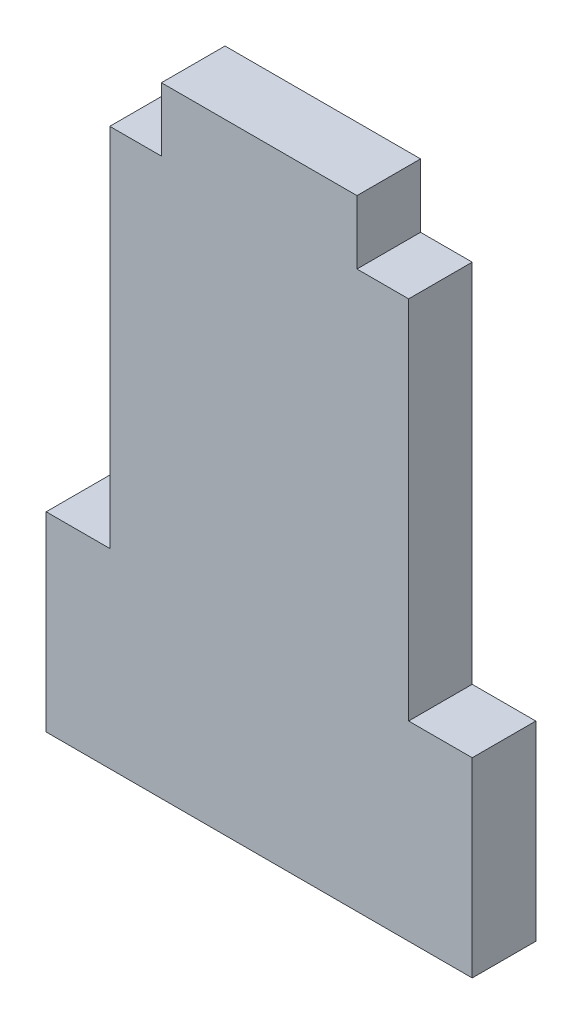
SolidWorks part; units mm, degrees
ref_plane "Ebene vorne" through (0, 0, 0) normal (0, 0, 1) x (1, 0, 0)
ref_plane "Ebene oben" through (0, 0, 0) normal (0, 1, 0) x (1, 0, 0)
ref_plane "Ebene rechts" through (0, 0, 0) normal (1, 0, 0) x (0, 0, -1)
sketch "Skizze1" plane through (0, 0, 0) normal (0, 0, 1) x (1, 0, 0)
  line L0 (0, 0) -> (0, 52.5861) construction
  line L4 (-13.4, 0) -> (-13.4, 12)
  line L5 (-13.4, 12) -> (-9.4, 12)
  line L6 (-9.4, 12) -> (-9.4, 35)
  line L7 (-9.4, 35) -> (-6.15, 35)
  line L8 (-6.15, 35) -> (-6.15, 39)
  line L9 (-6.15, 39) -> (6.15, 39)
  line L10 (6.15, 35) -> (6.15, 39)
  line L11 (9.4, 35) -> (6.15, 35)
  line L12 (9.4, 12) -> (9.4, 35)
  line L13 (13.4, 12) -> (9.4, 12)
  line L14 (13.4, 0) -> (13.4, 12)
  line L15 (-13.4, 0) -> (13.4, 0)
  point P15 (0, 39)
  dimension "D1" = 12
  dimension "D2" = 39
  dimension "D3" = 18.8
  dimension "D4" = 4
  dimension "D6" = 4
  dimension "D7" = 6.15
extrude "Aufsatz-Linear austragen1" add sketch "Skizze1" along normal blind 4
